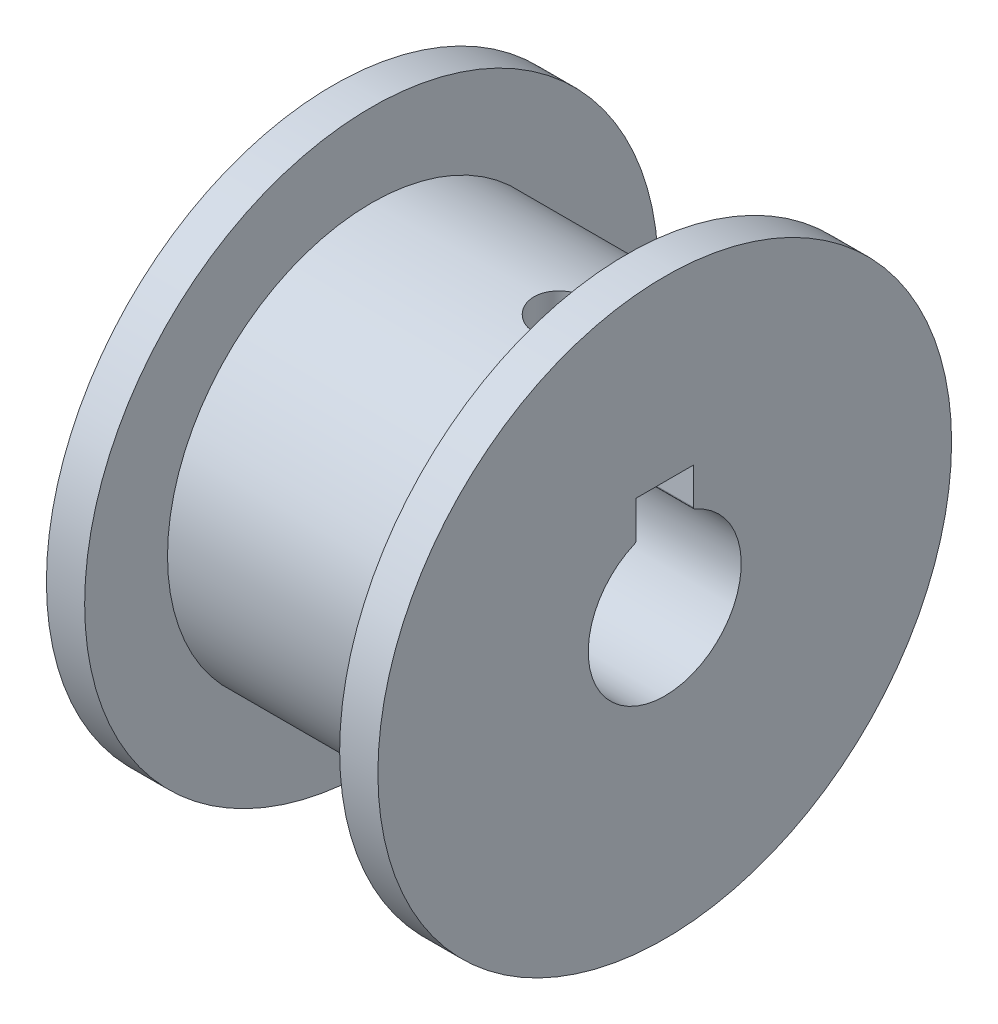
SolidWorks part; units mm, degrees
ref_plane "Piano frontale" through (0, 0, 0) normal (0, 0, 1) x (1, 0, 0)
ref_plane "Piano superiore" through (0, 0, 0) normal (0, 1, 0) x (1, 0, 0)
ref_plane "Piano destro" through (0, 0, 0) normal (1, 0, 0) x (0, 0, -1)
sketch "Sketch1" plane through (0, 0, 0) normal (1, 0, 0) x (0, 0, -1)
  circle A0 centre (0, 0) radius 16
  dimension "D1" = 32
extrude "Boss-Extrude1" add sketch "Sketch1" along normal blind 20
sketch "Sketch2" plane through (20, 0, 0) normal (1, 0, 0) x (0, 0, -1)
  line L0 (0, 4.7697) -> (0, 16) construction
  line L1 (0, 8.5621) -> (0, 4.7697) construction
  line L2 (-2.25, 8.5621) -> (2.25, 8.5621)
  line L3 (-2.25, 8.5621) -> (-2.25, 5.6954)
  line L5 (2.25, 8.5621) -> (2.25, 5.6954)
  arc A0 (-2.371, 5.5117) -> (2.371, 5.5117) centre (0, 0) ccw
  circle A1 centre (0, 0) radius 16 construction
  arc A2 (-2.371, 5.5117) -> (-2.25, 5.6954) centre (-2.45, 5.6954) ccw
  arc A3 (2.371, 5.5117) -> (2.25, 5.6954) centre (2.45, 5.6954) cw
  point P14 (-2.25, 5.5621)
  dimension "D1" = 12
  dimension "D4" = 0.2
  dimension "D5" = 0.2
  dimension "D2" = 4.5
  dimension "D3" = 3
sketch "Sketch3" plane through (20, 0, 0) normal (1, 0, 0) x (0, 0, -1)
  circle A0 centre (0, 0) radius 22.5
  dimension "D1" = 45
extrude "Boss-Extrude2" add sketch "Sketch3" along normal blind 3
sketch "Sketch4" plane through (0, 0, 0) normal (-1, 0, 0) x (0, 0, 1)
  circle A0 centre (0, 0) radius 22.5
  dimension "D1" = 45
extrude "Boss-Extrude3" add sketch "Sketch4" along normal blind 3
extrude "Cut-Extrude2" cut sketch "Sketch2" against normal blind 25 and the other way blind 3
sketch "Sketch6" plane through (0, 8.5621, 0) normal (0, -1, 0) x (1, 0, 0)
  line L0 (-3, 0) -> (23, 0) construction
  line L1 (-3, -2.25) -> (-3, 2.25) construction
  line L2 (23, -2.25) -> (23, 2.25) construction
  circle A0 centre (15, 0) radius 2.25
  point P8 (16.8381, 0)
  dimension "D1" = 4.5
  dimension "D2" = 8
extrude "Cut-Extrude3" cut sketch "Sketch6" against normal blind 10
